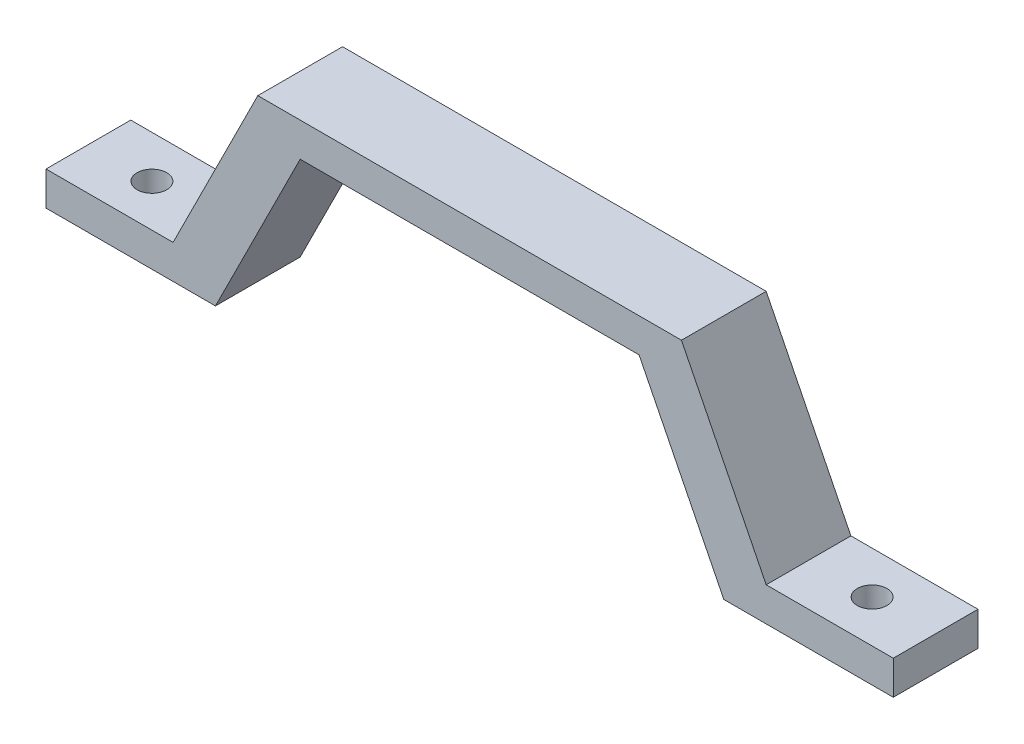
SolidWorks part; units mm, degrees
ref_plane "Front Plane" through (0, 0, 0) normal (0, 0, 1) x (1, 0, 0)
ref_plane "Top Plane" through (0, 0, 0) normal (0, 1, 0) x (1, 0, 0)
ref_plane "Right Plane" through (0, 0, 0) normal (1, 0, 0) x (0, 0, -1)
sketch "Sketch1" plane through (0, 0, 0) normal (0, 0, 1) x (1, 0, 0)
  line L0 (35, 4) -> (25, 24)
  line L1 (20, 20) -> (30, 0)
  line L2 (20, 20) -> (-20, 20)
  line L3 (-20, 20) -> (-30, 0)
  line L4 (-30, 0) -> (-50, 0)
  line L5 (-50, 0) -> (-50, 4)
  line L6 (-50, 4) -> (-35, 4)
  line L7 (-35, 4) -> (-25, 24)
  line L8 (-25, 24) -> (25, 24)
  line L9 (50, 4) -> (35, 4)
  line L10 (50, 0) -> (50, 4)
  line L11 (30, 0) -> (50, 0)
  line L13 (0, 0) -> (0, 43.6726) construction
  point P1 (0, 20)
  point P11 (0, 24)
  dimension "D1" = 50
  dimension "D2" = 20
  dimension "D3" = 15
  dimension "D4" = 4
  dimension "D5" = 20
  dimension "D6" = 24
  dimension "D7" = 20
extrude "Boss-Extrude1" add sketch "Sketch1" along normal blind 10
sketch "Sketch2" plane through (0, 4, 0) normal (0, 1, 0) x (1, 0, 0)
  line L0 (-50, -10) -> (-50, 0) construction
  circle A0 centre (42.5, -5) radius 1.75
  circle A1 centre (-42.5, -5) radius 1.75
  point P7 (-50, -5)
  dimension "D1" = 3.5
  dimension "D2" = 3.5
  dimension "D3" = 85
  dimension "D4" = 42.5
extrude "Cut-Extrude1" cut sketch "Sketch2" against normal through all
